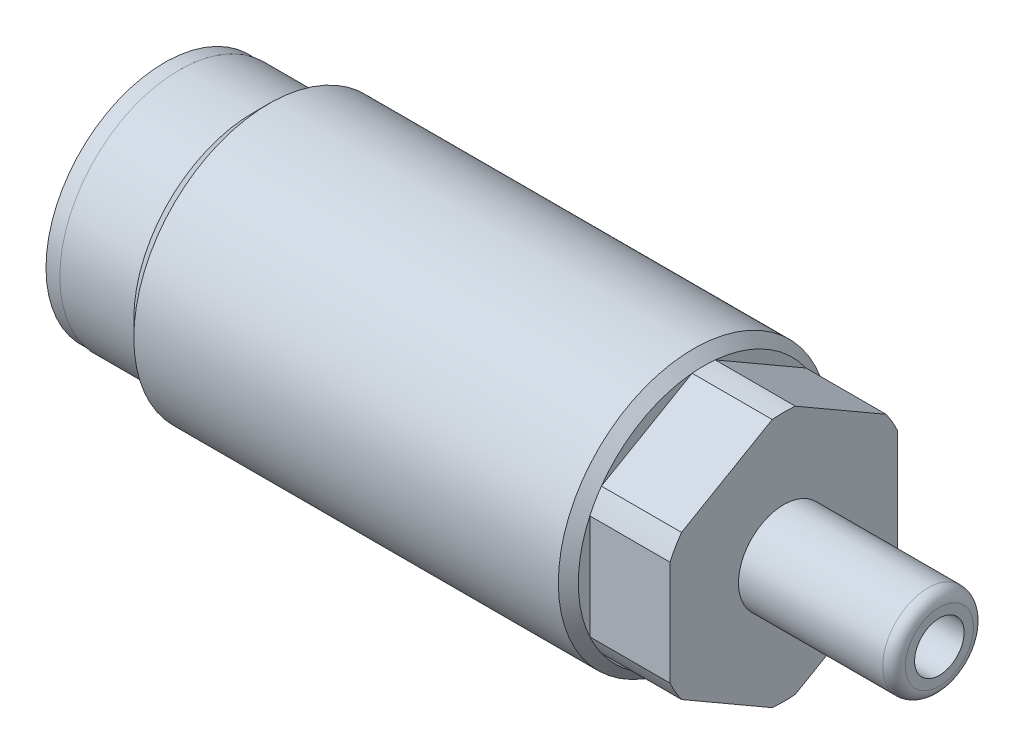
SolidWorks part; units mm, degrees
material "Alloy Steel"
ref_plane "Front Plane" through (0, 0, 0) normal (0, 0, 1) x (1, 0, 0)
ref_plane "Top Plane" through (0, 0, 0) normal (0, 1, 0) x (1, 0, 0)
ref_plane "Right Plane" through (0, 0, 0) normal (1, 0, 0) x (0, 0, -1)
sketch "Sketch1" plane through (0, 0, 0) normal (0, 0, 1) x (1, 0, 0)
  line L0 (-25.9547, 0) -> (83.8239, 0) construction
  line L2 (0, 0) -> (42.164, 0)
  line L3 (0, 0) -> (0, 9.4361)
  line L4 (0, 9.4361) -> (42.164, 9.4361)
  line L5 (42.164, 0) -> (42.164, 9.4361)
  dimension "D1" = 42.164
  dimension "D2" = 18.8722
revolve "Revolve1" add sketch "Sketch1" angle 360 about L0
sketch "Sketch2" plane through (0, 0, 0) normal (0, 0, 1) x (1, 0, 0)
  line L0 (-4.4239, 0) -> (47.9998, 0) construction
  line L1 (0, 9.4361) -> (0, -9.4361) construction
  line L2 (0, 0) -> (1.016, 0)
  line L3 (0, 0) -> (0, 3.9624)
  line L4 (0, 3.9624) -> (1.016, 3.9624)
  line L5 (1.016, 0) -> (1.016, 3.9624)
  dimension "D1" = 1.016
  dimension "D2" = 7.9248
revolve "Cut-Revolve1" cut sketch "Sketch2" angle 360 about L0
sketch "Sketch3" plane through (0, 0, 0) normal (0, 0, 1) x (1, 0, 0)
  line L0 (-2.1466, 0) -> (43.3996, 0) construction
  line L1 (0, 8.3185) -> (5.1562, 8.3185)
  line L2 (0, 9.4361) -> (0, -9.4361) construction
  line L3 (5.1562, 8.3185) -> (6.2738, 9.4361)
  line L4 (42.164, 9.4361) -> (0, 9.4361) construction
  line L5 (6.2738, 9.4361) -> (0, 9.4361)
  line L6 (0, 9.4361) -> (0, 8.3185)
  dimension "D1" = 5.1562
  dimension "D2" = 45
  dimension "D3" = 16.637
revolve "Cut-Revolve2" cut sketch "Sketch3" angle 360 about L0
cosmetic thread "Cosmetic Thread1" parameters "D2"=15.637
sketch "Sketch4" plane through (0, 0, 0) normal (0, 0, 1) x (1, 0, 0)
  line L0 (-3.3274, 0) -> (46.7209, 0) construction
  line L1 (42.164, 8.7376) -> (36.576, 8.7376)
  line L2 (42.164, -9.4361) -> (42.164, 9.4361) construction
  line L3 (36.576, 8.7376) -> (35.8775, 9.4361)
  line L4 (42.164, 9.4361) -> (6.2738, 9.4361) construction
  line L5 (35.8775, 9.4361) -> (42.164, 9.4361)
  line L6 (42.164, 9.4361) -> (42.164, 8.7376)
  dimension "D1" = 5.588
  dimension "D2" = 45
  dimension "D3" = 17.4752
revolve "Cut-Revolve3" cut sketch "Sketch4" angle 360 about L0
sketch "Sketch5" plane through (42.164, 0, 0) normal (1, 0, 0) x (0, 0, -1)
  line L0 (0, 10.1439) -> (0, -10.6187) construction
  line L1 (0, 9.1654) -> (7.9375, 4.5827)
  line L2 (7.9375, 4.5827) -> (7.9375, -4.5827)
  line L3 (0, -9.1654) -> (7.9375, -4.5827)
  line L4 (0, -9.1654) -> (-7.9375, -4.5827)
  line L5 (0, 9.1654) -> (-7.9375, 4.5827)
  line L6 (-7.9375, -4.5827) -> (-7.9375, 4.5827)
  circle A0 centre (0, 0) radius 7.9375
  circle M1 centre (0, 0) radius 8.7376
  dimension "D1" = 15.875
  dimension "D2" = 120
  dimension "D3" = 120
extrude "Cut-Extrude1" cut sketch "Sketch5" against normal blind 5.588 contours L6 M1 | L5 M1 | L1 M1 | L2 M1 | L3 M1 | L4 M1
sketch "Sketch6" plane through (0, 0, 0) normal (0, 0, 1) x (1, 0, 0)
  line L0 (-1.6911, 0) -> (45.1759, 0) construction
  line L1 (42.164, -3.6526) -> (42.164, 3.6526) construction
  line L2 (42.164, 0) -> (53.0098, 0)
  line L3 (42.164, 0) -> (42.164, 3.1623)
  line L4 (42.164, 3.1623) -> (53.0098, 3.1623)
  line L5 (53.0098, 0) -> (53.0098, 3.1623)
  line L6 (0, 8.3185) -> (0, -8.3185) construction
  dimension "D1" = 53.0098
  dimension "D2" = 6.3246
revolve "Revolve3" add sketch "Sketch6" angle 360 about L0
fillet "Fillet1" radius 0.7874 1 edges at (53.0098, 0, 3.1623)
hole_wizard "#8-32 Tapped Hole1" positions "Sketch11" profile "Sketch10" tap size "#8-32" standard "ANSI Inch"
sketch "Sketch11" plane through (53.0098, 0, 0) normal (1, 0, 0) x (0, 0, -1)
  point P0 (0, 0)
sketch "Sketch10" plane through (53.0098, 0, 0) normal (0, 1, 0) x (0, 0, -1)
  line L0 (0, 0) -> (0, 11.7058)
  line L1 (0, 11.7058) -> (1.7272, 10.668)
  line L2 (1.7272, 10.668) -> (1.7272, 0)
  line L5 (1.7272, 0) -> (0, 0)
  line L10 (0, 11.7058) -> (-1.7272, 10.668) construction
  line L11 (0, -6.35) -> (0, 107.95) construction
  dimension "Tap Drill Dia." = 3.4544
  dimension "Tap Drill Depth" = 10.668
  dimension "Drill Angle" = 118
cosmetic thread "Hole Thread1" parameters "D1"=6.35, "D2"=4.1656
sketch "Sketch12" plane through (0, 0, 0) normal (0, 0, 1) x (1, 0, 0)
  line L0 (0, 8.3185) -> (0, -8.3185) construction
  line L1 (0, 8.2677) -> (-1.016, 8.2677)
  line L2 (0, 8.2677) -> (0, 5.7404)
  line L3 (0, 5.7404) -> (-1.016, 5.7404)
  line L4 (-1.016, 8.2677) -> (-1.016, 5.7404)
  line L5 (-4.8071, 0) -> (58.9695, 0) construction
  dimension "D1" = 1.016
  dimension "D2" = 16.5354
  dimension "D3" = 11.4808
revolve "Revolve4" add sketch "Sketch12" angle 360 about L5
